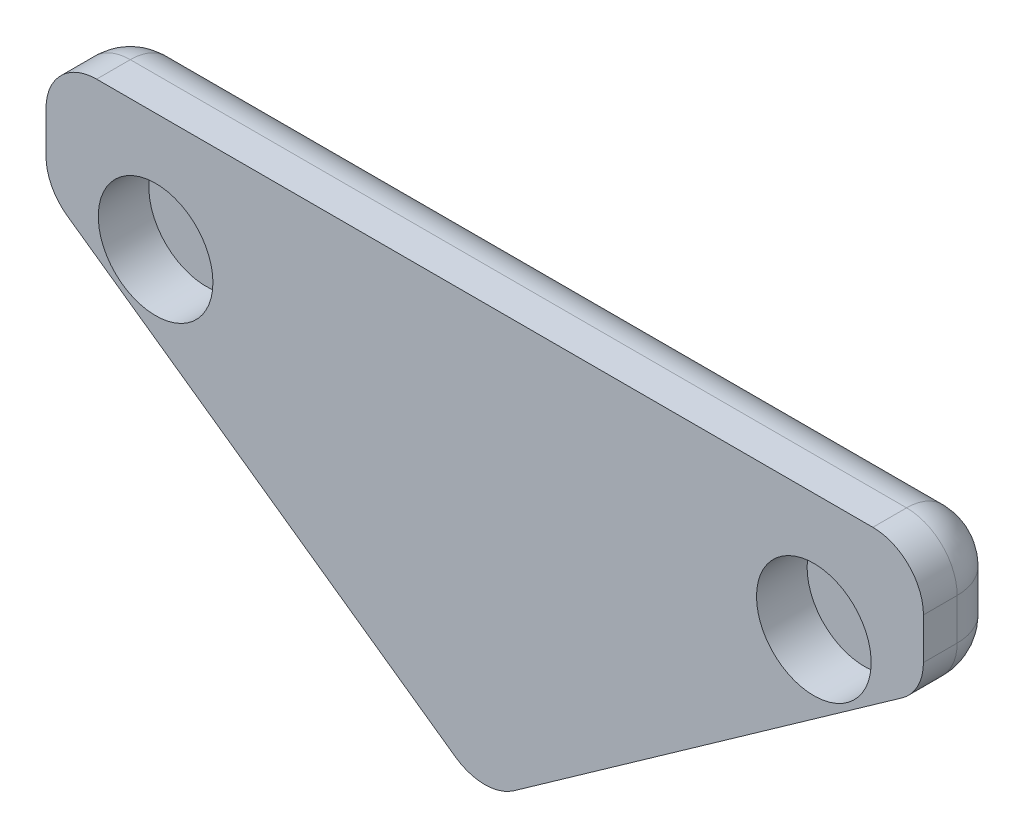
SolidWorks part; units mm, degrees
ref_plane "Front Plane" through (0, 0, 0) normal (0, 0, 1) x (1, 0, 0)
ref_plane "Top Plane" through (0, 0, 0) normal (0, 1, 0) x (1, 0, 0)
ref_plane "Right Plane" through (0, 0, 0) normal (1, 0, 0) x (0, 0, -1)
sketch "Sketch1" plane through (0, 0, 0) normal (0, 0, 1) x (1, 0, 0)
  line L0 (-7.5642, 12.7) -> (-7.5642, 9.2)
  line L3 (-7.5642, 9.2) -> (5.4458, 0)
  line L4 (5.4458, 0) -> (5.4458, 12.7)
  line L6 (5.4458, 12.7) -> (-7.5642, 12.7)
  line L7 (-4.3142, 12.7) -> (-4.3142, 6.884) construction
  line L8 (-7.5642, 9.2) -> (5.4458, 9.2) construction
  dimension "D1" = 3.5
  dimension "D2" = 3.25
  dimension "D3" = 12.7
  dimension "D5" = 13.01
extrude "Boss-Extrude1" add sketch "Sketch1" along normal blind 2.5
sketch "Sketch2" plane through (0, 0, 2.5) normal (0, 0, 1) x (1, 0, 0)
  line L0 (-7.5642, 9.2) -> (5.4458, 9.2) construction
  line L1 (-7.5642, 12.7) -> (-7.5642, 9.2) construction
  line L2 (5.4458, 0) -> (5.4458, 12.7) construction
  line L3 (-4.3142, 12.7) -> (-4.3142, 0) construction
  line L4 (5.4458, 12.7) -> (-7.5642, 12.7) construction
  circle A0 centre (-4.3142, 9.2) radius 1.7
  dimension "D1" = 3.5
  dimension "D2" = 3.25
extrude "Cut-Extrude1" cut sketch "Sketch2" against normal blind 1.5
mirror "Mirror2" about plane through (5.4458, 0, 2.5) normal (-1, 0, 0) of bodies 103
fillet "Fillet1" radius 1.5 10 edges at (-7.5642, 12.7, 1.25) (-7.5642, 10.95, 0) (5.4458, 12.7, 0) (-1.0592, 4.6, 0) (-7.5642, 9.2, 1.25) (5.4458, 0, 1.25) (18.4558, 10.95, 0) (18.4558, 12.7, 1.25) (18.4558, 9.2, 1.25) (11.9508, 4.6, 0)
